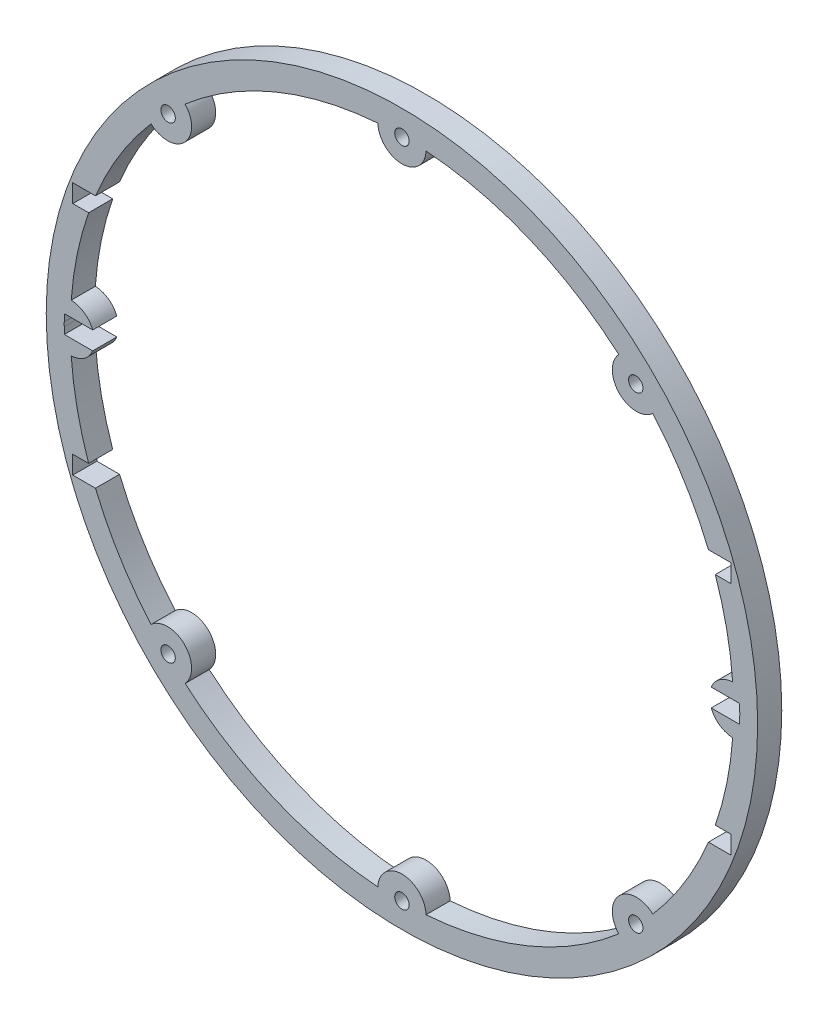
SolidWorks part; units mm, degrees
material "6061-T6 (SS)"
ref_plane "Front Plane" through (0, 0, 0) normal (0, 0, 1) x (1, 0, 0)
ref_plane "Top Plane" through (0, 0, 0) normal (0, 1, 0) x (1, 0, 0)
ref_plane "Right Plane" through (0, 0, 0) normal (1, 0, 0) x (0, 0, -1)
sketch "Sketch1" plane through (0, 0, 0) normal (0, 0, 1) x (1, 0, 0)
  line L0 (-57.15, 70.156) -> (57.15, 70.156) construction
  line L1 (0, 90.4875) -> (0, -90.4875) construction
  line L2 (90.2424, 6.656) -> (-90.2424, 6.656) construction
  line L3 (-69.85, -57.5236) -> (69.85, -57.5236) construction
  circle A0 centre (0, 0) radius 90.4875 construction
  circle A1 centre (0, 0) radius 93.6625
  circle A2 centre (0, 0) radius 87.3125
  dimension "D1" = 180.975
  dimension "D2" = 114.3
  dimension "D3" = 63.5
  dimension "D4" = 139.7
  dimension "D5" = 3.175
  dimension "D6" = 3.175
extrude "Boss-Extrude1" add sketch "Sketch1" along normal blind 6.35
sketch "Sketch3" plane through (0, 0, 6.35) normal (0, 0, 1) x (1, 0, 0)
  line L0 (0, 0) -> (-61.7393, 61.7393) construction
  line L1 (0, 0) -> (61.7393, 61.7393) construction
  line L2 (0, 87.3125) -> (0, -87.3125) construction
  line L3 (-87.3125, 0) -> (87.3125, 0) construction
  arc A0 (-6.3458, 87.0816) -> (6.3458, 87.0816) centre (0, 87.3125) ccw
  circle A1 centre (0, 0) radius 87.3125 construction
  arc A2 (-66.0631, 57.0888) -> (-57.0888, 66.0631) centre (-61.7393, 61.7393) ccw
  arc A3 (87.0816, -6.3458) -> (87.0816, 6.3458) centre (87.3125, 0) cw
  arc A4 (6.3458, -87.0816) -> (-6.3458, -87.0816) centre (0, -87.3125) ccw
  arc A5 (-87.0816, -6.3458) -> (-87.0816, 6.3458) centre (-87.3125, 0) ccw
  arc A6 (57.0888, -66.0631) -> (66.0631, -57.0888) centre (61.7393, -61.7393) cw
  arc A7 (57.0888, 66.0631) -> (66.0631, 57.0888) centre (61.7393, 61.7393) ccw
  arc A8 (-66.0631, -57.0888) -> (-57.0888, -66.0631) centre (-61.7393, -61.7393) cw
  circle M2 centre (0, 0) radius 87.3125
  dimension "D1" = 6.35
  dimension "D2" = 6.35
  dimension "D3" = 6.35
  dimension "D4" = 6.35
  dimension "D5" = 6.35
extrude "Boss-Extrude2" add sketch "Sketch3" against normal through all contours A2 M2 | A0 M2 | A7 M2 | A3 M2 | A6 M2 | A4 M2 | A8 M2 | A5 M2
sketch "Sketch4" plane through (0, 0, 6.35) normal (0, 0, 1) x (1, 0, 0)
  line L0 (0, 93.6625) -> (0, -93.6625) construction
  line L1 (-86.6775, 33.3375) -> (86.6775, 33.3375)
  line L2 (-86.6775, 33.3375) -> (-86.6775, 28.575)
  line L3 (-86.6775, 28.575) -> (86.6775, 28.575)
  line L4 (86.6775, 33.3375) -> (86.6775, 28.575)
  line L5 (0, 33.3375) -> (0, 28.575) construction
  line L6 (0, -28.575) -> (0, -33.3375) construction
  line L7 (88.9, 2.3813) -> (-88.9, 2.3812)
  line L8 (88.9, 2.3813) -> (88.9, -2.3812)
  line L9 (88.9, -2.3812) -> (-88.9, -2.3813)
  line L10 (-88.9, 2.3812) -> (-88.9, -2.3813)
  line L11 (88.9, 2.3813) -> (-88.9, -2.3813) construction
  line L12 (88.9, -2.3812) -> (-88.9, 2.3812) construction
  line L13 (-86.6775, -28.575) -> (86.6775, -28.575)
  line L14 (-86.6775, -28.575) -> (-86.6775, -33.3375)
  line L15 (-86.6775, -33.3375) -> (86.6775, -33.3375)
  line L16 (86.6775, -28.575) -> (86.6775, -33.3375)
  circle A1 centre (0, 0) radius 93.6625 construction
  point P4 (0, 0)
  dimension "D1" = 4.7625
  dimension "D2" = 173.355
  dimension "D3" = 28.575
  dimension "D4" = 4.7625
  dimension "D5" = 177.8
  dimension "D6" = 4.7625
  dimension "D7" = 173.355
  dimension "D8" = 28.575
extrude "Cut-Extrude2" cut sketch "Sketch4" against normal blind 6.35
hole_wizard "#6 Clearance Hole1" positions "Sketch6" profile "Sketch5" hole size "#6" standard "Ansi Inch"
sketch "Sketch6" plane through (0, 0, 6.35) normal (0, 0, 1) x (1, 0, 0)
  line L0 (-87.0816, -6.3458) -> (-87.0816, 6.3458) construction
  line L2 (-66.0631, 57.0888) -> (-57.0888, 66.0631) construction
  line L3 (-6.3458, 87.0816) -> (6.3458, 87.0816) construction
  line L4 (57.0888, 66.0631) -> (66.0631, 57.0888) construction
  line L5 (87.0816, 6.3458) -> (87.0816, -6.3458) construction
  line L6 (66.0631, -57.0888) -> (57.0888, -66.0631) construction
  line L7 (6.3458, -87.0816) -> (-6.3458, -87.0816) construction
  line L8 (-57.0888, -66.0631) -> (-66.0631, -57.0888) construction
  point P8 (-87.0816, 0)
  point P19 (-61.576, 61.576)
  point P22 (0, 87.0816)
  point P25 (61.576, 61.576)
  point P28 (87.0816, 0)
  point P31 (61.576, -61.576)
  point P34 (0, -87.0816)
  point P37 (-61.576, -61.576)
  dimension "D1" = 8
sketch "Sketch5" plane through (-87.0816, 0, 6.35) normal (1, 0, 0) x (0, -1, 0)
  line L0 (0, 0) -> (0, 26.5408)
  line L1 (0, 26.5408) -> (1.8986, 25.4)
  line L2 (1.8986, 25.4) -> (1.8986, 0)
  line L5 (1.8986, 0) -> (0, 0)
  line L10 (0, 26.5408) -> (-1.8986, 25.4) construction
  line L11 (0, -6.35) -> (0, 107.95) construction
  dimension "Hole Dia." = 3.7973
  dimension "Hole Depth" = 25.4
  dimension "Drill Angle" = 118
